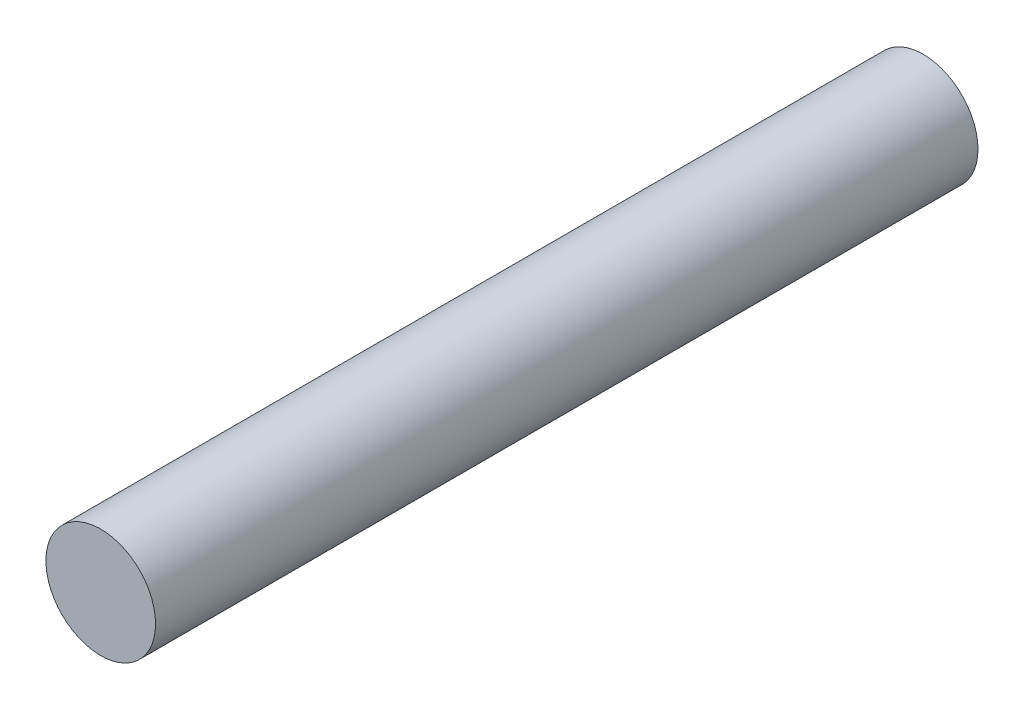
SolidWorks part; units mm, degrees
ref_plane "Alzado" through (0, 0, 0) normal (0, 0, 1) x (1, 0, 0)
ref_plane "Planta" through (0, 0, 0) normal (0, 1, 0) x (1, 0, 0)
ref_plane "Vista lateral" through (0, 0, 0) normal (1, 0, 0) x (0, 0, -1)
sketch "Croquis1" plane through (0, 0, 0) normal (0, 0, 1) x (1, 0, 0)
  circle A0 centre (0, 0) radius 4
extrude "Saliente-Extruir1" add sketch "Croquis1" along normal blind 60
